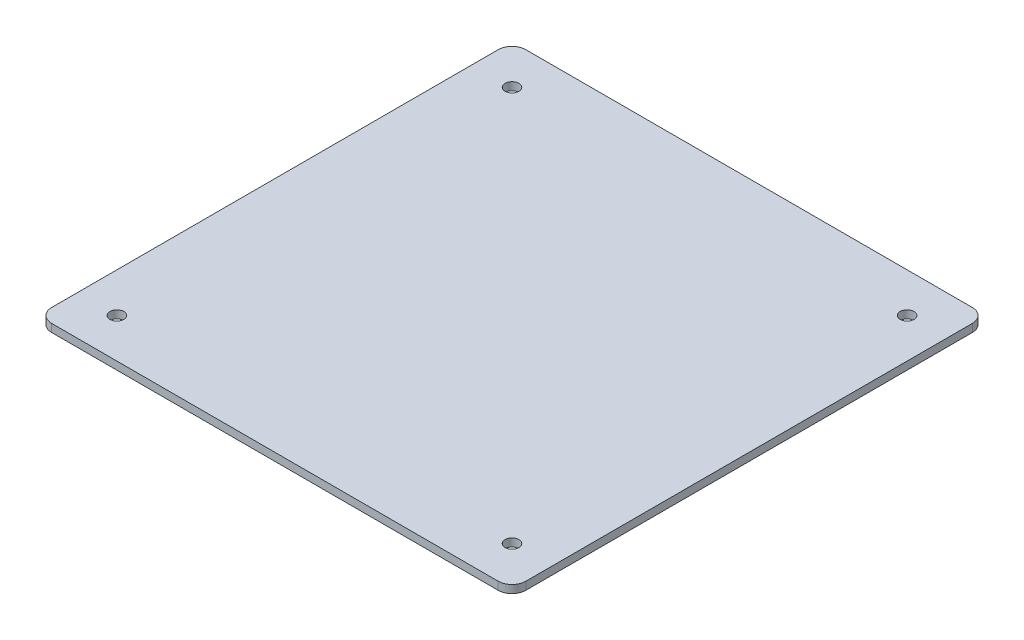
SolidWorks part; units mm, degrees
ref_plane "前视基准面" through (0, 0, 0) normal (0, 0, 1) x (1, 0, 0)
ref_plane "上视基准面" through (0, 0, 0) normal (0, 1, 0) x (1, 0, 0)
ref_plane "右视基准面" through (0, 0, 0) normal (1, 0, 0) x (0, 0, -1)
sketch "草图4" plane through (0, 0, 0) normal (0, 1, 0) x (1, 0, 0)
  line L1 (-60, 60) -> (60, 60)
  line L2 (-60, 60) -> (-60, -60)
  line L3 (-60, -60) -> (60, -60)
  line L4 (60, 60) -> (60, -60)
  line L5 (-60, 60) -> (60, -60) construction
  line L6 (-60, -60) -> (60, 60) construction
  point P0 (0, 0)
  dimension "D1" = 120
  dimension "D2" = 120
extrude "凸台-拉伸2" add sketch "草图4" along normal blind 2
fillet "圆角2" radius 3.5 4 edges at (-60, 1, -60) (60, 1, -60) (-60, 1, 60) (60, 1, 60)
sketch "草图5" plane through (0, 2, 0) normal (0, 1, 0) x (1, 0, 0)
  line L0 (-88.6063, 0) -> (124.8989, 0) construction
  line L1 (0, 129.1156) -> (0, -178.9068) construction
  line L3 (-50, 50) -> (50, 50) construction
  line L4 (-50, 50) -> (-50, -50) construction
  line L5 (-50, -50) -> (50, -50) construction
  line L6 (50, 50) -> (50, -50) construction
  line L7 (-50, 50) -> (50, -50) construction
  line L8 (-50, -50) -> (50, 50) construction
  circle A0 centre (-50, 50) radius 1.75
  circle A1 centre (-50, -50) radius 1.75
  circle A2 centre (50, -50) radius 1.75
  circle A3 centre (50, 50) radius 1.75
  point P5 (0, 0)
  dimension "D3" = 3.5
  dimension "D1" = 100
  dimension "D2" = 100
extrude "切除-拉伸1" cut sketch "草图5" against normal through all
